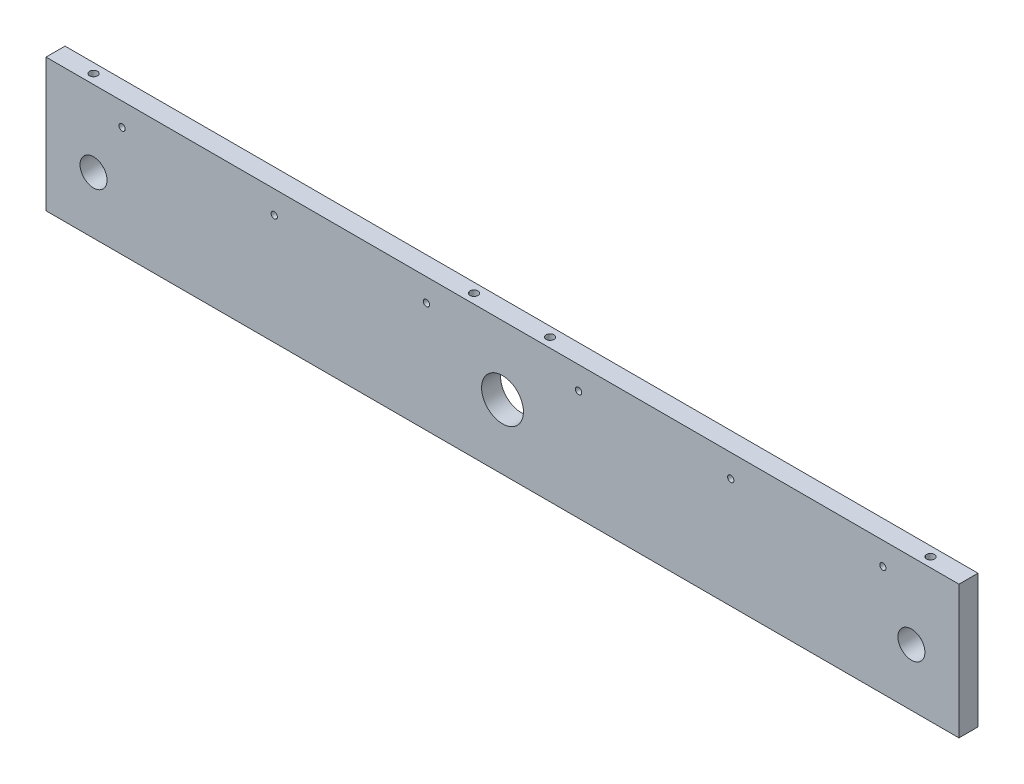
SolidWorks part; units mm, degrees
ref_plane "Front Plane" through (0, 0, 0) normal (0, 0, 1) x (1, 0, 0)
ref_plane "Top Plane" through (0, 0, 0) normal (0, 1, 0) x (1, 0, 0)
ref_plane "Right Plane" through (0, 0, 0) normal (1, 0, 0) x (0, 0, -1)
sketch "Sketch1" plane through (0, 0, 0) normal (0, 0, 1) x (1, 0, 0)
  line L0 (0, 35) -> (0, -35) construction
  line L1 (-240, 35) -> (240, 35)
  line L2 (-240, 35) -> (-240, -35)
  line L3 (-240, -35) -> (240, -35)
  line L4 (240, 35) -> (240, -35)
  line L5 (-240, 35) -> (240, -35) construction
  line L6 (-240, -35) -> (240, 35) construction
  circle A0 centre (0, -1) radius 11
  circle A1 centre (-215, -5) radius 7.1
  circle A2 centre (215, -5) radius 7.1
  point P0 (0, 0)
  point P19 (-110.5223, -5)
  point P20 (110.7229, 5.8856)
  point P21 (138.2211, -5)
  point P22 (-127.4089, -5)
  point P34 (146.7595, -19.5719)
  dimension "D3" = 22
  dimension "D4" = 14.2
  dimension "D5" = 36
  dimension "D1" = 480
  dimension "D2" = 70
  dimension "D6" = 40
extrude "Boss-Extrude1" add sketch "Sketch1" along normal blind 10
hole_wizard "M5 Tapped Hole1" positions "Sketch3" profile "Sketch4" tap size "M5" standard "ISO"
sketch "Sketch3" plane through (0, 35, 0) normal (0, 1, 0) x (1, 0, 0)
  line L0 (-240, -5) -> (240, -5) construction
  line L1 (-240, -10) -> (-240, 0) construction
  line L2 (240, -10) -> (240, 0) construction
  line L4 (0, 0) -> (0, -10) construction
  line L5 (240, 0) -> (-240, 0) construction
  line L6 (240, -10) -> (-240, -10) construction
  point P15 (-220, -5)
  point P18 (-20, -5)
  point P22 (20, -5)
  point P23 (220, -5)
  dimension "D1" = 20
  dimension "D2" = 20
sketch "Sketch4" plane through (220, 35, 5) normal (1, 0, 0) x (0, 0, 1)
  line L0 (0, 0) -> (0, 11.2618)
  line L1 (0, 11.2618) -> (2.1, 10)
  line L2 (2.1, 10) -> (2.1, 0)
  line L5 (2.1, 0) -> (0, 0)
  line L10 (0, 11.2618) -> (-2.1, 10) construction
  line L11 (0, -6.35) -> (0, 107.95) construction
  dimension "Tap Drill Dia." = 4.2
  dimension "Tap Drill Depth" = 10
  dimension "Drill Angle" = 118
cosmetic thread "Hole Thread1" parameters "D1"=10, "D2"=5
cosmetic thread "Hole Thread2" parameters "D1"=10, "D2"=5
cosmetic thread "Hole Thread3" parameters "D1"=10, "D2"=5
cosmetic thread "Hole Thread4" parameters "D1"=10, "D2"=5
hole_wizard "M5 Tapped Hole2" positions "Sketch5" profile "Sketch6" tap size "M5" standard "ISO"
sketch "Sketch5" plane through (0, -35, 0) normal (0, -1, 0) x (-1, 0, 0)
  line L0 (240, -5) -> (-240, -5) construction
  line L1 (240, -10) -> (240, 0) construction
  line L2 (-240, -10) -> (-240, 0) construction
  line L4 (0, -10) -> (0, 0) construction
  line L5 (240, -10) -> (-240, -10) construction
  point P17 (220, -5)
  point P21 (-220, -5)
  dimension "D1" = 20
sketch "Sketch6" plane through (220, -35, 5) normal (1, 0, 0) x (0, 0, -1)
  line L0 (0, 0) -> (0, 13.6618)
  line L1 (0, 13.6618) -> (2.1, 12.4)
  line L2 (2.1, 12.4) -> (2.1, 0)
  line L5 (2.1, 0) -> (0, 0)
  line L10 (0, 13.6618) -> (-2.1, 12.4) construction
  line L11 (0, -6.35) -> (0, 107.95) construction
  dimension "Tap Drill Dia." = 4.2
  dimension "Tap Drill Depth" = 12.4
  dimension "Drill Angle" = 118
cosmetic thread "Hole Thread5" parameters "D1"=10, "D2"=5
cosmetic thread "Hole Thread6" parameters "D1"=10, "D2"=5
hole_wizard "Ø3.3 (3.3) Diameter Hole1" positions "Sketch7" profile "Sketch8" hole size "Ø3.3" standard "ISO" end condition through all
sketch "Sketch7" plane through (0, 0, 10) normal (0, 0, 1) x (1, 0, 0)
  line L0 (240, 35) -> (-240, 35) construction
  line L1 (-240, 35) -> (-240, -35) construction
  point P0 (-200, 23)
  point P12 (-120, 23)
  point P13 (-40, 23)
  point P14 (40, 23)
  point P15 (120, 23)
  point P16 (200, 23)
  dimension "D1" = 12
  dimension "D2" = 40
  dimension "D3" = 6
sketch "Sketch8" plane through (-200, 23, 10) normal (1, 0, 0) x (0, -1, 0)
  line L0 (0, 0) -> (0, 10)
  line L1 (0, 10) -> (1.65, 10)
  line L2 (1.65, 10) -> (1.65, 0)
  line L5 (1.65, 0) -> (0, 0)
  line L11 (0, -6.35) -> (0, 107.95) construction
  dimension "Thru Hole Dia." = 3.3
  dimension "Thru Hole Depth" = 10
